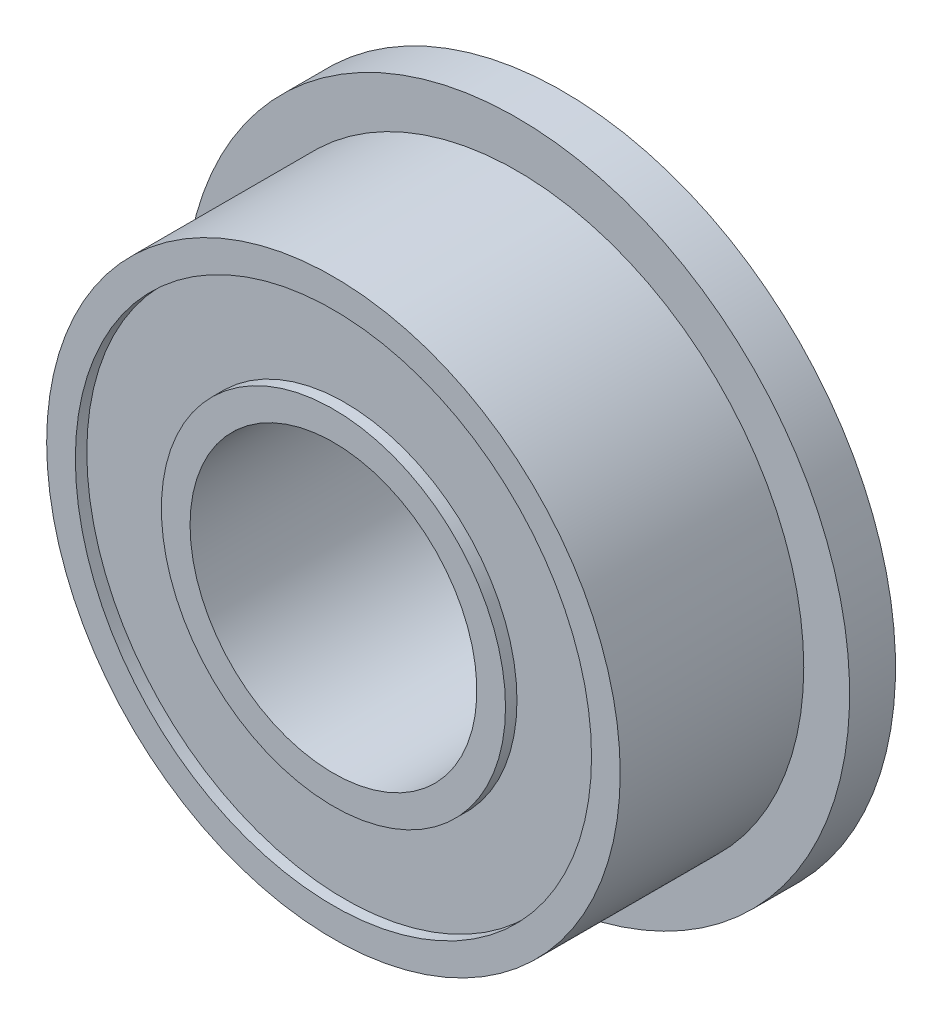
SolidWorks part; units mm, degrees
ref_plane "前基準面" through (0, 0, 0) normal (0, 0, 1) x (1, 0, 0)
ref_plane "上基準面" through (0, 0, 0) normal (0, 1, 0) x (1, 0, 0)
ref_plane "右基準面" through (0, 0, 0) normal (1, 0, 0) x (0, 0, -1)
sketch "草圖1" plane through (0, 0, 0) normal (0, 0, 1) x (1, 0, 0)
  circle A0 centre (0, 0) radius 5
  dimension "D1" = 10
extrude "填料-伸長1" add sketch "草圖1" along normal blind 4
sketch "草圖2" plane through (0, 0, 0) normal (0, 0, -1) x (-1, 0, 0)
  circle A0 centre (0, 0) radius 5.8
  dimension "D1" = 11.6
extrude "填料-伸長2" add sketch "草圖2" against normal blind 0.8
sketch "草圖3" plane through (0, 0, 0) normal (0, 0, -1) x (-1, 0, 0)
  circle A0 centre (0, 0) radius 2.5
  dimension "D1" = 5
extrude "除料-伸長1" cut sketch "草圖3" against normal through all
sketch "草圖4" plane through (0, 0, 0) normal (0, 0, -1) x (-1, 0, 0)
  circle A0 centre (0, 0) radius 5.1
  circle A1 centre (0, 0) radius 3.3
  circle A2 centre (0, 0) radius 2.5 construction
  dimension "D1" = 0.8
  dimension "D2" = 1.8
extrude "除料-伸長3" cut sketch "草圖4" against normal blind 0.2
sketch "草圖5" plane through (0, 0, 4) normal (0, 0, 1) x (1, 0, 0)
  circle A0 centre (0, 0) radius 3
  circle A1 centre (0, 0) radius 4.5
  circle A2 centre (0, 0) radius 2.5 construction
  dimension "D1" = 0.5
  dimension "D2" = 1.5
extrude "除料-伸長4" cut sketch "草圖5" against normal blind 0.2
